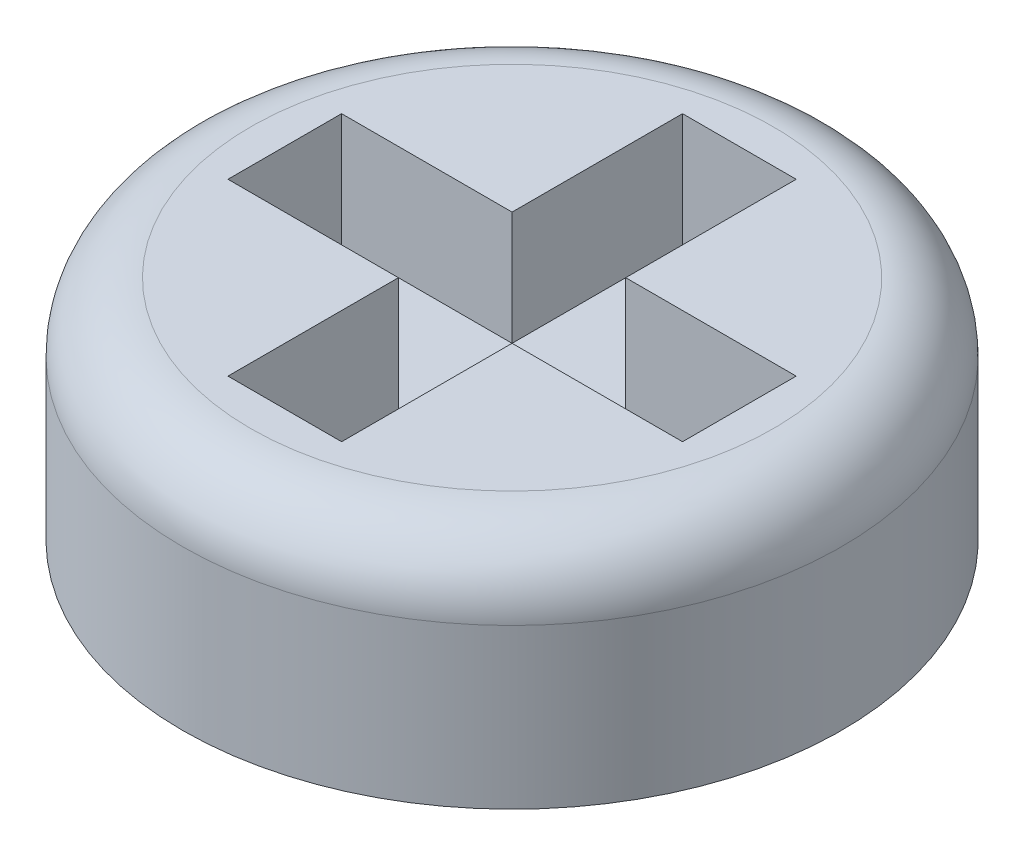
SolidWorks part; units mm, degrees
ref_plane "Front Plane" through (0, 0, 0) normal (0, 0, 1) x (1, 0, 0)
ref_plane "Top Plane" through (0, 0, 0) normal (0, 1, 0) x (1, 0, 0)
ref_plane "Right Plane" through (0, 0, 0) normal (1, 0, 0) x (0, 0, -1)
sketch "Sketch1" plane through (0, 0, 0) normal (0, 1, 0) x (1, 0, 0)
  circle A0 centre (0, 0) radius 1.45
  dimension "D1" = 2.9
extrude "Boss-Extrude1" add sketch "Sketch1" along normal blind 1
sketch "Sketch2" plane through (0, 1, 0) normal (0, 1, 0) x (1, 0, 0)
  line L0 (-0.25, 0.25) -> (-0.25, 1)
  line L1 (0.25, -1) -> (-0.25, -1)
  line L2 (0.25, -1) -> (0.25, -0.25)
  line L3 (0.25, 1) -> (-0.25, 1)
  line L4 (-0.25, -1) -> (-0.25, -0.25)
  line L5 (0.25, -1) -> (-0.25, 1) construction
  line L6 (0.25, 1) -> (-0.25, -1) construction
  line L7 (1, -0.25) -> (0.25, -0.25)
  line L8 (1, -0.25) -> (1, 0.25)
  line L9 (1, 0.25) -> (0.25, 0.25)
  line L10 (-1, -0.25) -> (-1, 0.25)
  line L11 (1, -0.25) -> (-1, 0.25) construction
  line L12 (1, 0.25) -> (-1, -0.25) construction
  line L13 (-0.25, -0.25) -> (-1, -0.25)
  line L14 (0.25, 0.25) -> (0.25, 1)
  line L15 (-0.25, 0.25) -> (-1, 0.25)
  point P0 (0, 0)
  point P6 (0, 0)
  dimension "D1" = 0.5
  dimension "D2" = 2
  dimension "D3" = 0.5
  dimension "D4" = 2
extrude "Cut-Extrude1" cut sketch "Sketch2" against normal blind 0.5
fillet "Fillet3" radius 0.3 1 edges at (0, 1, 1.45)
